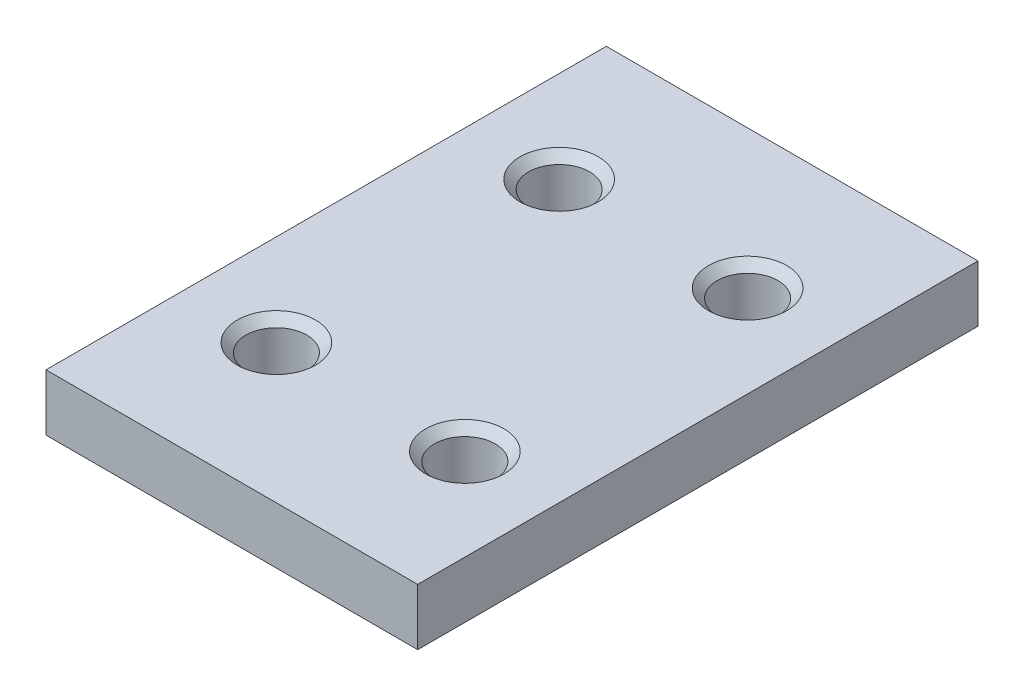
SolidWorks part; units mm, degrees
material "ABS"
ref_plane "Front Plane" through (0, 0, 0) normal (0, 0, 1) x (1, 0, 0)
ref_plane "Top Plane" through (0, 0, 0) normal (0, 1, 0) x (1, 0, 0)
ref_plane "Right Plane" through (0, 0, 0) normal (1, 0, 0) x (0, 0, -1)
sketch "Sketch1" plane through (0, 0, 0) normal (0, 1, 0) x (1, 0, 0)
  line L1 (0, 0) -> (-42.7203, 0)
  line L2 (0, 0) -> (0, -64.4)
  line L3 (0, -64.4) -> (-42.7203, -64.4)
  line L4 (-42.7203, 0) -> (-42.7203, -64.4)
  dimension "D1" = 42.7203
  dimension "D2" = 64.4
extrude "Boss-Extrude1" add sketch "Sketch1" along normal blind 6.5
sketch "Sketch2" plane through (0, 6.5, 0) normal (0, 1, 0) x (1, 0, 0)
  line L0 (-42.7203, -32.2) -> (0, -32.2) construction
  line L1 (-42.7203, 0) -> (-42.7203, -64.4) construction
  line L2 (0, -64.4) -> (0, 0) construction
  line L3 (-21.3601, 0) -> (-21.3601, -64.4) construction
  line L4 (0, 0) -> (-42.7203, 0) construction
  line L5 (-42.7203, -64.4) -> (0, -64.4) construction
  line L6 (-43.0203, -32.35) -> (-43.0203, 0) construction
  line L7 (0.3, -32.2) -> (0.3, 0) construction
  line L8 (-42.7203, 0) -> (-21.3601, 0) construction
  line L9 (-21.3601, 0) -> (0.3, 0) construction
  line L10 (-32.1902, 1.2139) -> (-32.1902, -64.4) construction
  line L11 (-10.5301, 1.2139) -> (-10.5301, -64.4)
  line L12 (-53.0203, 0.3) -> (0.3, 0.3) construction
  line L13 (0.7216, 0.3) -> (0.7216, -32.2)
  line L14 (0.7216, -15.95) -> (-42.7203, -15.95)
  line L15 (-43.0203, 1.2139) -> (-21.3601, 1.2139)
  line L16 (-21.3601, 1.2139) -> (0.3, 1.2139)
  circle A0 centre (-32.1902, -15.95) radius 3.5
  circle A1 centre (-10.5301, -15.95) radius 3.5
  circle A2 centre (-10.5301, -48.45) radius 3.5
  circle A3 centre (-32.1902, -48.45) radius 3.5
  point P16 (-32.0402, 0)
  point P17 (-10.5301, 0)
  point P26 (0.7216, -15.95)
  point P36 (-10.5301, 1.2139)
  point P38 (-12.2122, 1.0639)
  point P40 (-32.1902, 1.2139)
  dimension "D4" = 7
  dimension "D1" = 43.3203
  dimension "D2" = 32.5
  dimension "D3" = 0.4216
  dimension "D5" = 0.9139
extrude "Cut-Extrude1" cut sketch "Sketch2" against normal through all contours L14 A0 | A1 L11 L14 | A1 L14 L11 | A1 L11 L14 | A1 L14 L11 | L14 A0 | A3 | L11 A2
chamfer "Chamfer1" distance 1 angle 45 4 edges at (-10.5301, 6.5, 51.95) (-32.1902, 6.5, 51.95) (-10.5301, 6.5, 19.45) (-32.1902, 6.5, 19.45)
